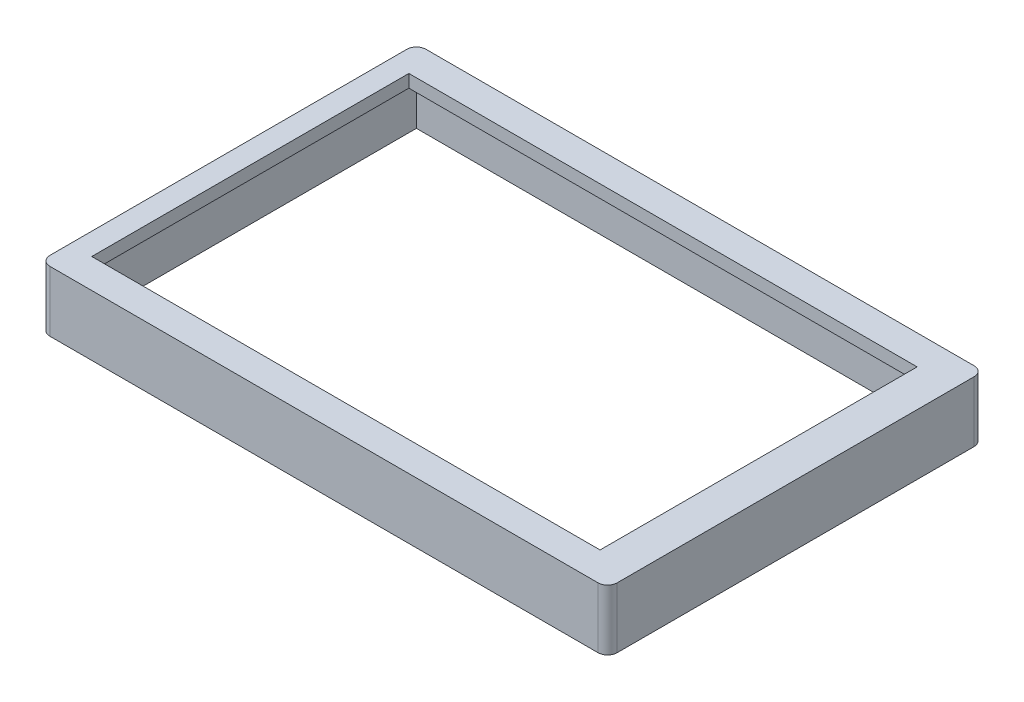
SolidWorks part; units mm, degrees
material "ABS"
ref_plane "Front Plane" through (0, 0, 0) normal (0, 0, 1) x (1, 0, 0)
ref_plane "Top Plane" through (0, 0, 0) normal (0, 1, 0) x (1, 0, 0)
ref_plane "Right Plane" through (0, 0, 0) normal (1, 0, 0) x (0, 0, -1)
sketch "Sketch1" plane through (0, 0, 0) normal (0, 1, 0) x (1, 0, 0)
  line L0 (-86.6348, 59) -> (91.3652, 59)
  line L2 (-79.75, 49.75) -> (79.75, 49.75)
  line L3 (-79.75, 49.75) -> (-79.75, -49.75)
  line L4 (-79.75, -49.75) -> (79.75, -49.75)
  line L5 (91.3652, 59) -> (91.3652, -59)
  line L6 (-86.6348, -59) -> (91.3652, -59)
  line L7 (-86.6348, 59) -> (-86.6348, -59)
  line L8 (79.75, 49.75) -> (79.75, -49.75)
  line L9 (-79.75, 49.75) -> (79.75, -49.75) construction
  line L10 (-79.75, -49.75) -> (79.75, 49.75) construction
  point P0 (0, 0)
  dimension "D1" = 178
  dimension "D2" = 118
  dimension "D3" = 59
  dimension "D4" = 91.3652
  dimension "D5" = 159.5
  dimension "D6" = 99.5
extrude "Boss-Extrude1" add sketch "Sketch1" along normal blind 4
sketch "Sketch2" plane through (0, 0, 0) normal (0, -1, 0) x (1, 0, 0)
  line L4 (-86.6348, 59) -> (-86.6348, -59)
  line L5 (-86.6348, -59) -> (91.3652, -59)
  line L6 (91.3652, -59) -> (91.3652, 59)
  line L7 (91.3652, 59) -> (-86.6348, 59)
  line L8 (-86.6348, 59) -> (-86.6348, -59)
  line L9 (-86.6348, -59) -> (91.3652, -59)
  line L10 (91.3652, -59) -> (91.3652, 59)
  line L11 (91.3652, 59) -> (-86.6348, 59)
  line L24 (-82.6348, 55) -> (-82.6348, -55)
  line L25 (-82.6348, -55) -> (87.3652, -55)
  line L26 (87.3652, -55) -> (87.3652, 55)
  line L27 (87.3652, 55) -> (-82.6348, 55)
  line L28 (-82.6348, 55) -> (-82.6348, -55)
  line L29 (-82.6348, -55) -> (87.3652, -55)
  line L30 (87.3652, -55) -> (87.3652, 55)
  line L31 (87.3652, 55) -> (-82.6348, 55)
  dimension "D1" = 0
  dimension "D2" = 4
extrude "Boss-Extrude2" add sketch "Sketch2" along normal blind 15
fillet "Fillet1" radius 3 4 edges at (-86.6348, -5.5, -59) (91.3652, -5.5, -59) (91.3652, -5.5, 59) (-86.6348, -5.5, 59)
